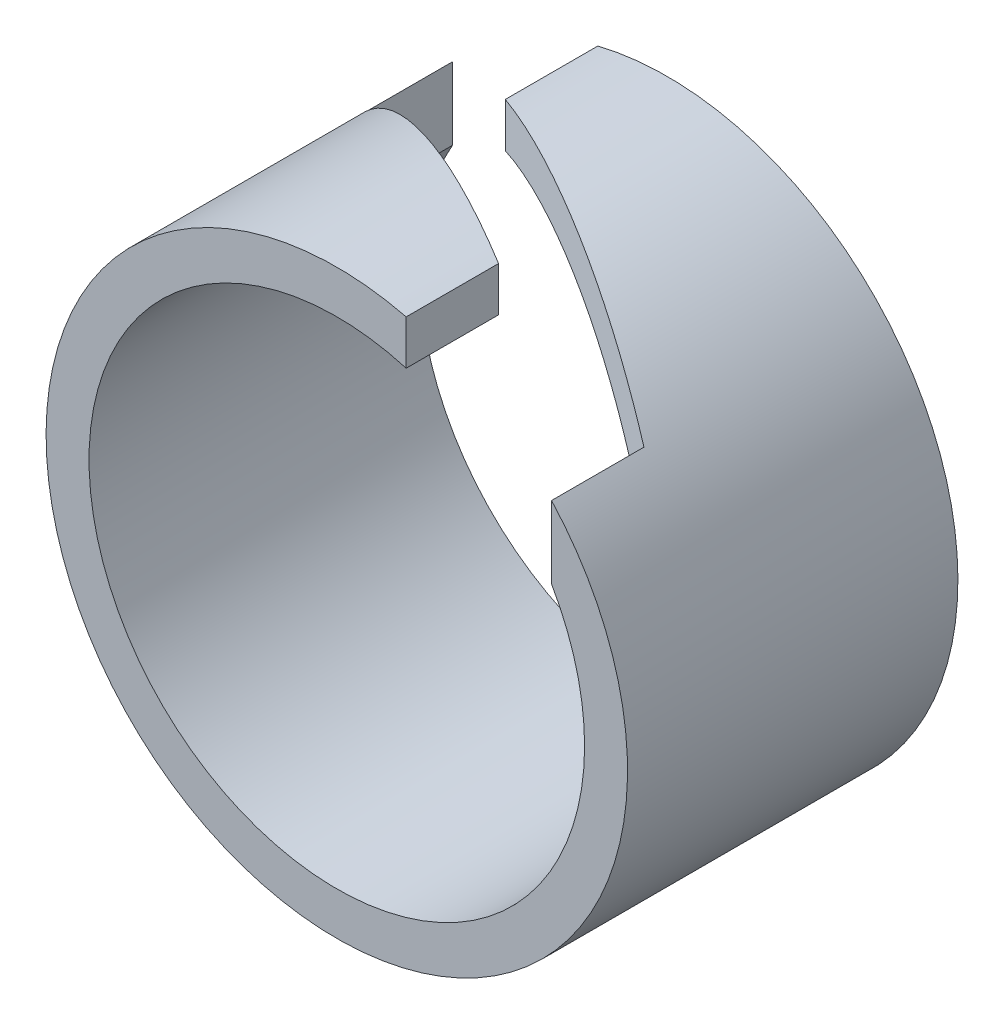
SolidWorks part; units mm, degrees
material "Zinc AC41A Alloy, As Cast"
ref_plane "Front Plane" through (0, 0, 0) normal (0, 0, 1) x (1, 0, 0)
ref_plane "Top Plane" through (0, 0, 0) normal (0, 1, 0) x (1, 0, 0)
ref_plane "Right Plane" through (0, 0, 0) normal (1, 0, 0) x (0, 0, -1)
sketch "Sketch2" plane through (0, 0, 0) normal (0, 0, 1) x (1, 0, 0)
  circle A0 centre (0, 0) radius 4.4
  circle A1 centre (0, 0) radius 3.75
  dimension "D1" = 7.5
  dimension "D2" = 8.8
extrude "Boss-Extrude1" add sketch "Sketch2" along normal blind 5
ref_plane "Plane1" through (0, 4.4, 0) normal (0, 1, 0) x (1, 0, 0)
sketch "Sketch3" plane through (0, 4.4, 0) normal (0, 1, 0) x (1, 0, 0)
  line L0 (1.05, -5) -> (3.25, -5)
  line L1 (-4.4, -5) -> (4.4, -5) construction
  line L2 (-3.25, 0) -> (-1.05, 0)
  line L4 (-1.05, 0) -> (-1.05, -5.2525) construction
  line L5 (-3.25, 0) -> (-3.25, -1.4) construction
  line L6 (-1.05, 0) -> (-1.05, -1.4) construction
  line L10 (3.25, -5) -> (3.25, -3.6018)
  line L11 (3.25, -3.6018) -> (-1.05, -1.4)
  line L12 (-1.05, 0) -> (-1.05, -1.4)
  line L13 (1.05, -5) -> (1.05, -3.6018)
  line L14 (1.05, -3.6018) -> (-3.25, -1.4)
  line L15 (-3.25, -1.4) -> (-3.25, 0)
  line L17 (0, -5) -> (0, -50000) construction
  point P5 (0, -5)
  point P11 (0, 0)
  point P20 (0, -5)
  dimension "D2" = 2.2
  dimension "D3" = 1.4
  dimension "D4" = 2.2
extrude "Cut-Extrude1" cut sketch "Sketch3" against normal blind 5
